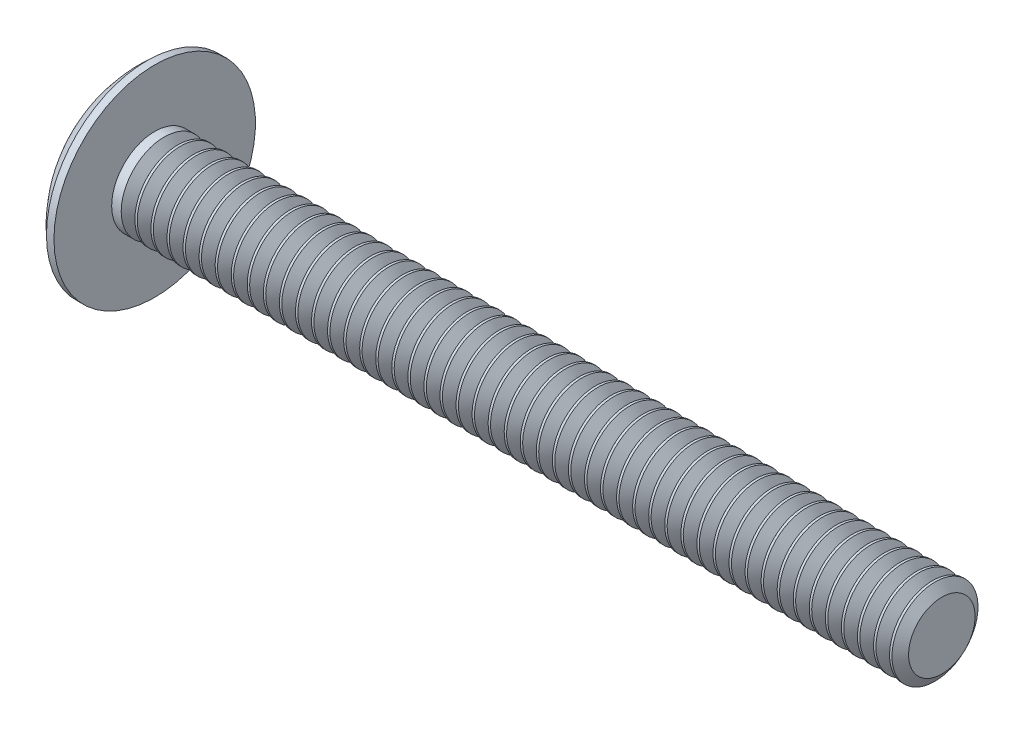
SolidWorks part; units mm, degrees
ref_plane "Plane1" through (0, 0, 0) normal (0, 0, 1) x (1, 0, 0)
ref_plane "Plane2" through (0, 0, 0) normal (0, 1, 0) x (1, 0, 0)
ref_plane "Plane3" through (0, 0, 0) normal (1, 0, 0) x (0, 0, -1)
sketch "BodySke" plane through (0, 0, 0) normal (0, 0, 1) x (1, 0, 0)
  line L0 (2.5908, 2.0828) -> (2.5908, 4.8768)
  line L1 (40.6908, 0) -> (0, 0)
  line L2 (-25.4, 0) -> (127, 0) construction
  line L3 (2.2279, -4.8768) -> (2.5908, -4.8768) construction
  line L4 (2.5908, 2.0828) -> (40.6908, 2.0828)
  line L5 (40.6908, 2.0828) -> (40.6908, 0)
  line L6 (2.2279, 4.8768) -> (2.5908, 4.8768)
  line L7 (2.5908, -2.0828) -> (40.6908, -2.0828) construction
  line L8 (3.3833, 3.6703) -> (3.3833, -5.8547) construction
  line L9 (2.5908, 6.35) -> (2.5908, -3.175) construction
  arc A0 (2.2279, 4.8768) -> (0, 0) centre (6.4516, 0) ccw
  dimension "Head_rad" = 6.4516
  dimension "Diameter" = 4.1656
  dimension "Length" = 38.1
  dimension "Head_ht" = 2.5908
  dimension "Head_dia" = 9.7536
  dimension "Advance" = 0.7925
  dimension "Thread_nom" = 38.1
revolve "Base-Revolve" add sketch "BodySke" angle 360 about L2
cosmetic thread "ThreadCosmetic" [suppressed] parameters "Thread_length"=37.3075, "Thread_minor"=3.2207
sketch "Sketch2" plane through (0, 0, 0) normal (1, 0, 0) x (0, 0, -1)
  line L0 (4.8768, -0.6858) -> (-4.8768, -0.6858)
  line L1 (4.8768, -0.6858) -> (4.8768, 0.6858)
  line L2 (-4.8768, 0.6858) -> (4.8768, 0.6858)
  line L3 (-4.8768, 0.6858) -> (-4.8768, -0.6858)
  dimension "D1" = 9.7536
  dimension "Slot_width" = 1.3716
  dimension "D2" = 4.8768
  dimension "D3" = 0.6858
extrude "Slot" [suppressed] cut sketch "Sketch2" along normal blind 1.4732
sketch "Sketch3" plane through (0, 0, 0) normal (1, 0, 0) x (0, 0, -1)
  line L0 (0.5207, -2.7305) -> (-0.5207, -2.7305)
  line L1 (0.5207, -2.7305) -> (0.5207, 2.7305)
  line L2 (-0.5207, 2.7305) -> (0.5207, 2.7305)
  line L3 (-0.5207, 2.7305) -> (-0.5207, -2.7305)
  dimension "Cross_width" = 1.0414
  dimension "Cross_dia" = 5.461
  dimension "D1" = 0.5207
  dimension "D2" = 2.7305
ref_plane "Plane4" through (3.0734, 0, 0) normal (1, 0, 0) x (0, 0, -1)
sketch "Sketch4" plane through (3.0734, 0, 0) normal (1, 0, 0) x (0, 0, -1)
  line L0 (0.2604, -0.2604) -> (-0.2603, -0.2604)
  line L1 (0.2604, -0.2604) -> (0.2604, 0.2604)
  line L2 (-0.2604, 0.2604) -> (0.2604, 0.2604)
  line L3 (-0.2604, 0.2604) -> (-0.2603, -0.2604)
  dimension "D1" = 0.5207
  dimension "D2" = 0.2604
  dimension "D3" = 0.5207
  dimension "D4" = 0.2604
loft "Cross" cut profiles "Sketch3", "Sketch4"
pattern_circular "CirPattern1" count 2 every 90 about axis through (0, 0, 0) along (1, 0, 0) of "Cross"
sketch "ThdSchSke" plane through (0, 0, 0) normal (0, 0, 1) x (1, 0, 0)
  line L0 (3.3833, -1.6104) -> (3.0525, -2.0828)
  line L1 (3.3833, -1.6104) -> (3.7141, -2.0828)
  line L2 (3.7141, -2.0828) -> (3.7141, -2.6035)
  line L3 (-3.175, 0) -> (5.1513, 0) construction
  line L5 (3.7141, -2.6035) -> (3.0525, -2.6035)
  line L6 (3.0525, -2.6035) -> (3.0525, -2.0828)
  dimension "Diameter" = 4.1656
  dimension "SideAngle" = 55
  dimension "VeeAngle" = 70
  dimension "Thread_minor" = 3.2207
  dimension "Overcut" = 5.207
  dimension "Start" = 3.3833
revolve "ThreadSchematic" cut sketch "ThdSchSke" angle 360 about L3
pattern_linear "ThdSchPat" count 49 spacing 0.7772 along (1, 0, 0) of "ThreadSchematic"
equation "\"D1@Sketch2\" = \"Head_dia@BodySke\""
equation "\"D2@Sketch2\" = \"D1@Sketch2\" / 2"
equation "\"D3@Sketch2\" = \"Slot_width@Sketch2\" / 2"
equation "\"D1@Sketch3\" = \"Cross_width@Sketch3\" / 2"
equation "\"D2@Sketch3\" = \"Cross_dia@Sketch3\" / 2"
equation "\"D1@Sketch4\" = \"Cross_width@Sketch3\" *.5"
equation "\"D2@Sketch4\" = \"D1@Sketch4\" / 2"
equation "\"D3@Sketch4\" = \"D1@Sketch4\""
equation "\"D4@Sketch4\" = \"D3@Sketch4\" / 2"
equation "\"Thread_length@ThreadCosmetic\" = ((sgn( (\"Length@BodySke\" - \"Advance@BodySke\" ) - \"Thread_nom@BodySke\" )-1)*( (\"Length@BodySke\" - \"Advance@BodySke\" ) - \"Thread_nom@BodySke\" ))/-2+ \"Thread_nom@BodySke\""
equation "\"Thread_minor@ThdSchSke\" = \"Thread_minor@ThreadCosmetic\""
equation "\"Diameter@ThdSchSke\" = \"Diameter@BodySke\""
equation "\"Overcut@ThdSchSke\" = \"Diameter@BodySke\" * 1.25"
equation "\"Start@ThdSchSke\" = \"Head_ht@BodySke\" + \"Length@BodySke\" - \"Thread_length@ThreadCosmetic\"  '---Non-countersunk---"
equation "\"Num_threads@ThdSchPat\" = int( \"Thread_length@ThreadCosmetic\" / \"Advance@BodySke\" + 0.999 )  + 1"
equation "\"Advance@ThdSchPat\" = \"Thread_length@ThreadCosmetic\" /  (\"Num_threads@ThdSchPat\" - 1) 'relax it"
